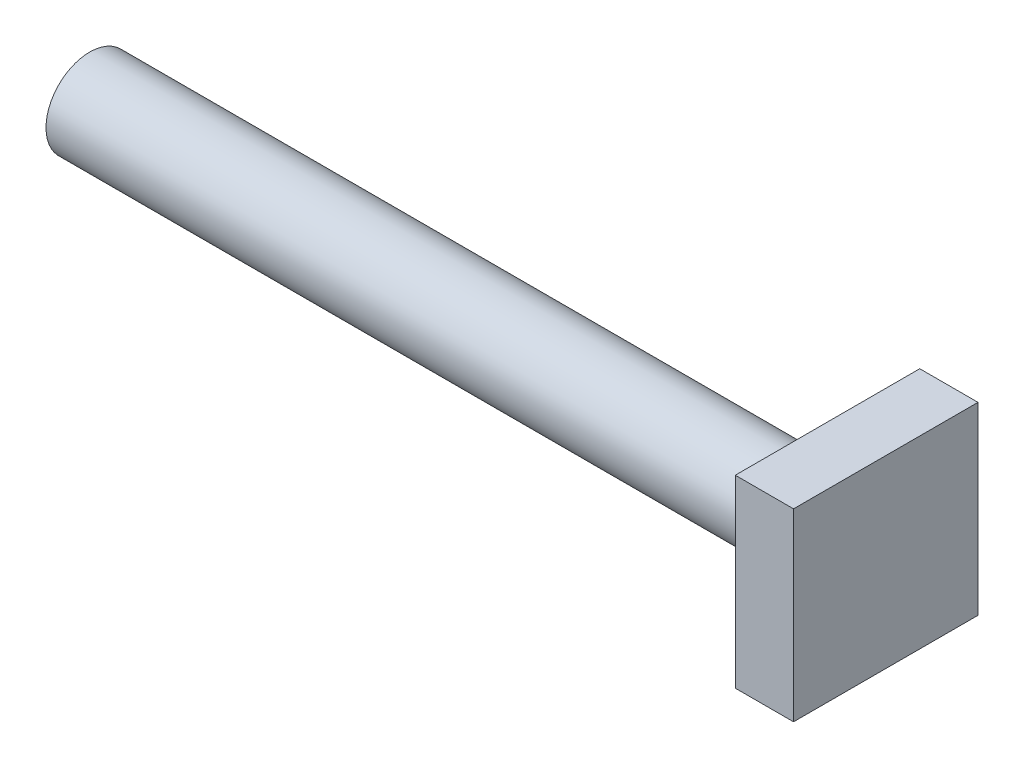
SolidWorks part; units mm, degrees
ref_plane "Front Plane" through (0, 0, 0) normal (0, 0, 1) x (1, 0, 0)
ref_plane "Top Plane" through (0, 0, 0) normal (0, 1, 0) x (1, 0, 0)
ref_plane "Right Plane" through (0, 0, 0) normal (1, 0, 0) x (0, 0, -1)
sketch "Sketch2" plane through (0, 0, 0) normal (1, 0, 0) x (0, 0, -1)
  line L1 (0, 0) -> (19, 0)
  line L2 (0, 0) -> (0, 19)
  line L3 (0, 19) -> (19, 19)
  line L4 (19, 0) -> (19, 19)
  dimension "D1" = 19
  dimension "D2" = 19
extrude "Boss-Extrude1" add sketch "Sketch2" along normal blind 6
sketch "Sketch3" plane through (0, 0, 0) normal (-1, 0, 0) x (0, 0, 1)
  line L1 (0, 19) -> (0, 0) construction
  line L2 (-19, 19) -> (0, 19) construction
  circle A0 centre (-9.5, 9.5) radius 4.5
  dimension "D1" = 9
  dimension "D2" = 9.5
  dimension "D3" = 9.5
extrude "Boss-Extrude2" add sketch "Sketch3" along normal blind 76
